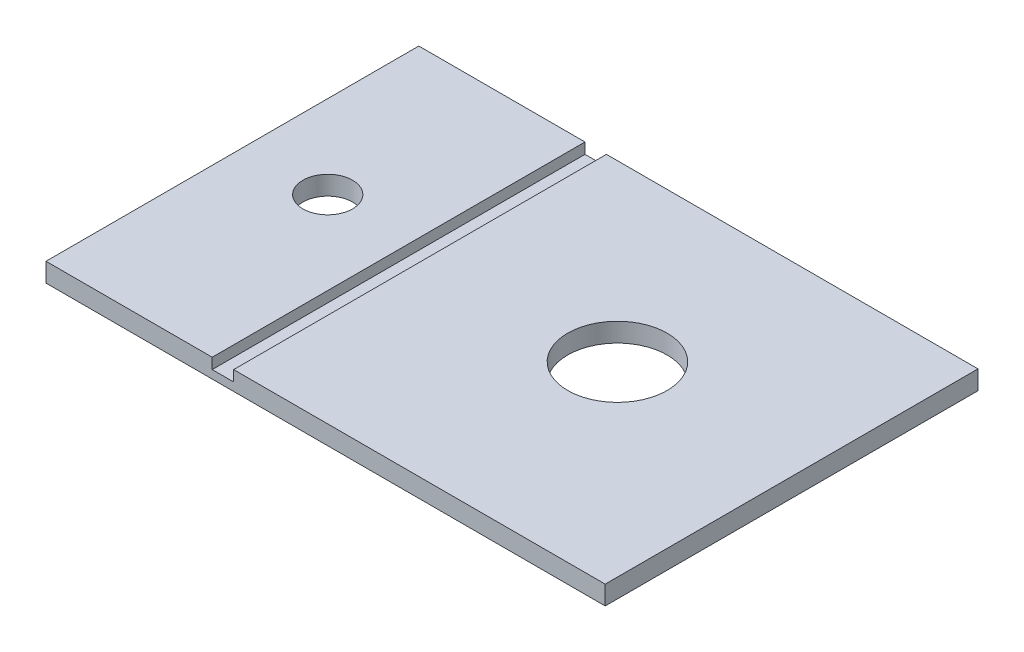
SolidWorks part; units mm, degrees
ref_plane "Plan de face" through (0, 0, 0) normal (0, 0, 1) x (1, 0, 0)
ref_plane "Plan de dessus" through (0, 0, 0) normal (0, 1, 0) x (1, 0, 0)
ref_plane "Plan de droite" through (0, 0, 0) normal (1, 0, 0) x (0, 0, -1)
sketch "Esquisse1" plane through (0, 0, 0) normal (0, 0, 1) x (1, 0, 0)
  line L0 (0, -20.1861) -> (0, 185.3139) construction
  line L1 (0, 45.0639) -> (-450, 45.0639)
  line L2 (0, 45.0639) -> (0, 60.3139)
  line L3 (0, 60.3139) -> (-450, 60.3139)
  line L4 (-450, 45.0639) -> (-450, 60.3139)
  dimension "D1" = 15.25
  dimension "D2" = 65.25
  dimension "D3" = 450
extrude "Boss.-Extru.1" add sketch "Esquisse1" along normal up to surface (300 mm away)
sketch "Esquisse2" plane through (0, 60.3139, 0) normal (0, 1, 0) x (1, 0, 0)
  line L0 (0, 0) -> (-450, 0) construction
  line L1 (-299, 0) -> (-316.25, 0)
  line L2 (-299, 0) -> (-299, -300)
  line L3 (-299, -300) -> (-316.25, -300)
  line L4 (-316.25, 0) -> (-316.25, -300)
  line L5 (0, -300) -> (-450, -300) construction
  dimension "D1" = 17.25
  dimension "D2" = 1
extrude "Enlèv. mat.-Extru.1" cut sketch "Esquisse2" against normal blind 8.625
sketch "Esquisse3" plane through (0, 60.3139, 0) normal (0, 1, 0) x (1, 0, 0)
  line L0 (-150, -140.1613) -> (-450, -140.1613) construction
  line L1 (-450, -300) -> (-450, 0) construction
  line L2 (-383.125, -300) -> (-383.125, 0) construction
  line L3 (-316.25, -300) -> (-450, -300) construction
  line L4 (-316.25, 0) -> (-450, 0) construction
  circle A0 centre (-150, -140.1613) radius 40
  circle A1 centre (-383.125, -140.1613) radius 20
  dimension "D1" = 80
  dimension "D2" = 40
extrude "Enlèv. mat.-Extru.2" cut sketch "Esquisse3" against normal up to next
